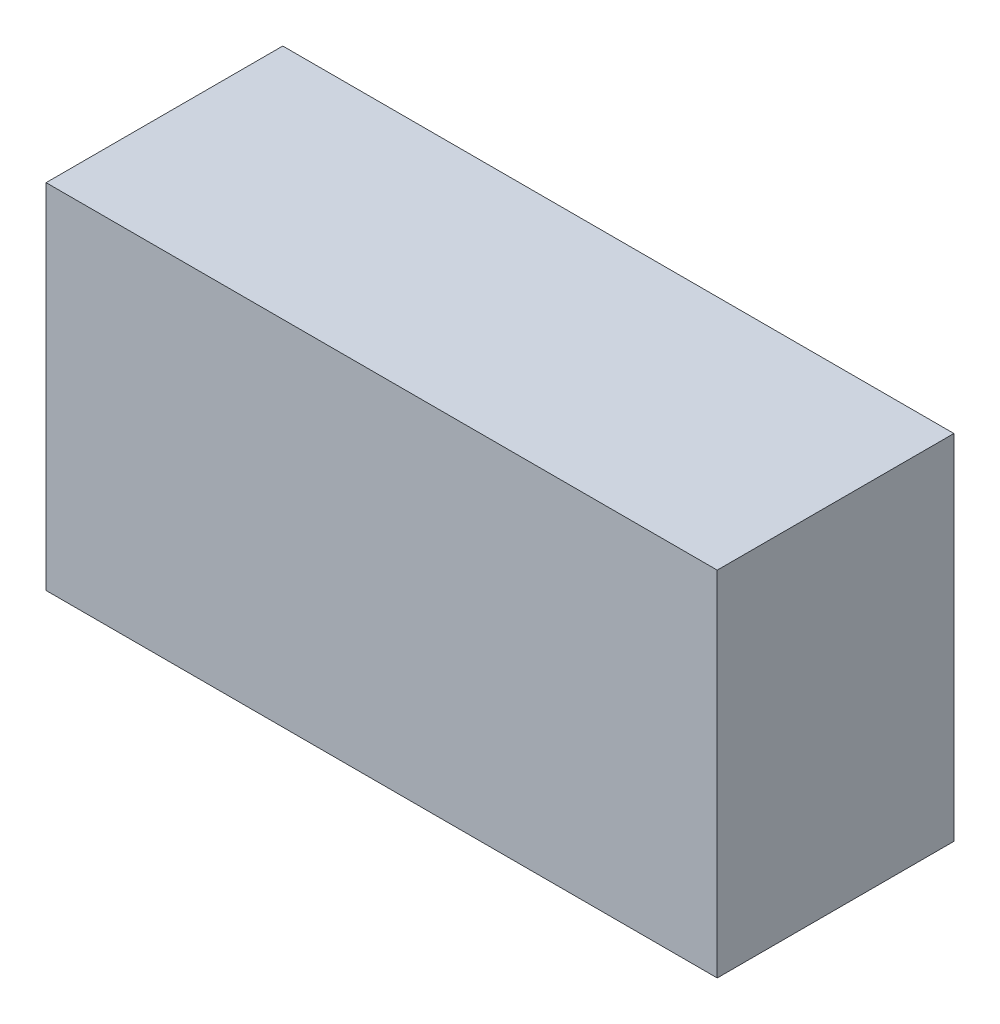
SolidWorks part; units mm, degrees
ref_plane "Front Plane" through (0, 0, 0) normal (0, 0, 1) x (1, 0, 0)
ref_plane "Top Plane" through (0, 0, 0) normal (0, 1, 0) x (1, 0, 0)
ref_plane "Right Plane" through (0, 0, 0) normal (1, 0, 0) x (0, 0, -1)
sketch "Sketch1" plane through (0, 0, 0) normal (0, 0, 1) x (1, 0, 0)
  line L1 (0, 0) -> (48.26, 0)
  line L2 (0, 0) -> (0, 25.4)
  line L3 (0, 25.4) -> (48.26, 25.4)
  line L4 (48.26, 0) -> (48.26, 25.4)
  dimension "D1" = 48.26
  dimension "D2" = 25.4
extrude "Boss-Extrude1" add sketch "Sketch1" along normal blind 17.018
